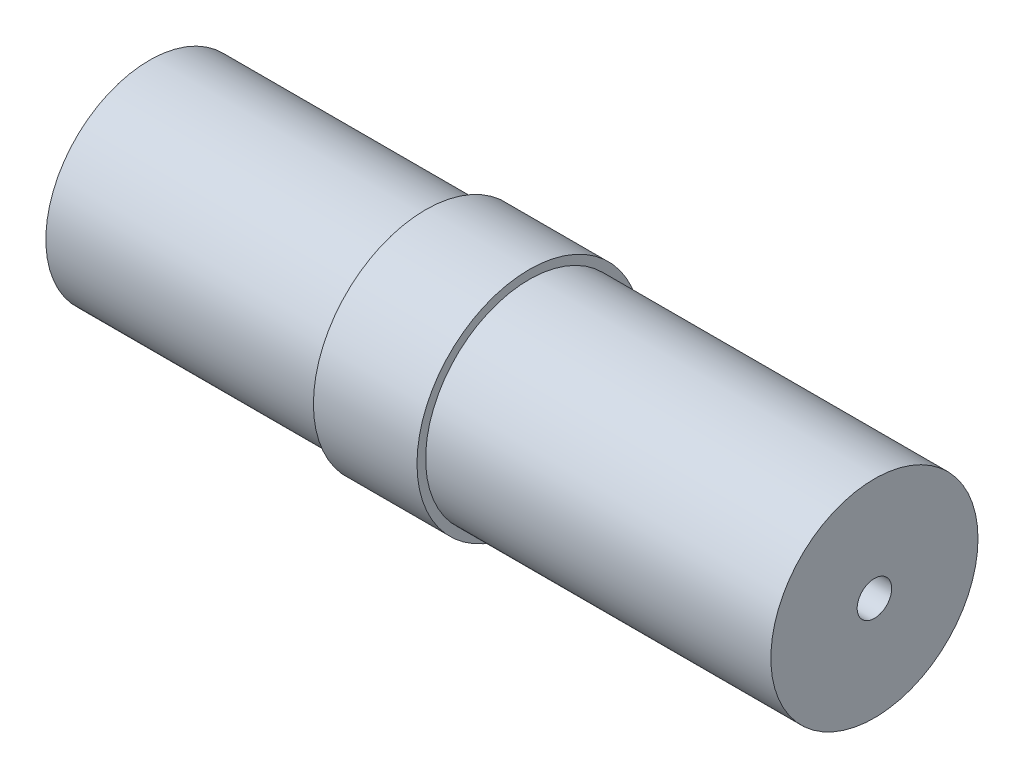
SolidWorks part; units mm, degrees
material "Tantalum"
ref_plane "Front Plane" through (0, 0, 0) normal (0, 0, 1) x (1, 0, 0)
ref_plane "Top Plane" through (0, 0, 0) normal (0, 1, 0) x (1, 0, 0)
ref_plane "Right Plane" through (0, 0, 0) normal (1, 0, 0) x (0, 0, -1)
sketch "Sketch1" plane through (0, 0, 0) normal (0, 0, 1) x (1, 0, 0)
  line L2 (11, 3.25) -> (-10, 3.25) construction
  line L3 (10, 0.5) -> (11, 0.5)
  line L4 (10, 0.5) -> (10, 2.25)
  line L5 (10, 2.25) -> (-10, 2.25)
  line L9 (-10, 2.25) -> (-10, 3.25) construction
  line L18 (1, 3.25) -> (1, 3)
  line L19 (1, 3) -> (11, 3)
  line L20 (11, 3) -> (11, 0.5)
  line L21 (1, 3) -> (-10, 3) construction
  line L22 (-2, 3.25) -> (-2, 3)
  line L23 (-10, 3) -> (-10, 2.25)
  line L24 (1, 3.25) -> (-2, 3.25)
  line L25 (-2, 3) -> (-10, 3)
  dimension "D1" = 3.25
  dimension "D2" = 2.75
  dimension "D3" = 1
  dimension "D4" = 1
  dimension "D5" = 0.25
  dimension "D6" = 10
  dimension "D7" = 8
  dimension "D8" = 3
  dimension "D9" = 20
ref_axis "Axis1" through (13.5, 0, 0) along (-1, 0, 0)
revolve "Revolve1" add sketch "Sketch1" angle 360 about axis through (13.5, 0, 0) along (-1, 0, 0)
other "#12-28 Machine Threads Stud1" [suppressed] parameters "D1"=5.4864, "D2"=10, "D3"=8, "D4"=6
sketch "Sketch15" plane through (-42.5, 0, 0) normal (0, 1, 0) x (0, 0, -1)
  line L5 (0, -14.3089) -> (0, 0) construction
  line L6 (2.2022, 0) -> (2.7432, -0.541)
  line L9 (2.7432, -0.541) -> (2.7432, -8)
  line L10 (2.2022, 0) -> (3, 0)
  line L11 (3, 0) -> (3, -8)
  line L12 (2.7432, -8) -> (3, -8)
  dimension "Minor Diameter" = 4.4044
  dimension "Major Diameter" = 5.4864
  dimension "Thread Length" = 8
  dimension "Cylinder Diameter" = 6
  dimension "Chamfer Angle" = 45
cosmetic thread "Stud Thread1" [suppressed] parameters "D1"=8, "D2"=4.4044
thread "Thread5" [suppressed] pitch 0.8 start angle 0, offset 0, length 8, pitch 0.8, diameter 5.4864
ref_plane "Plane6" through (-41.959, 0, -2.7432) normal (0, -1, 0) x (0, 0, -1)
sketch "Thread Profile6" plane through (-41.959, 0, -2.7432) normal (0, -1, 0) x (0, 0, -1)
  line L0 (0, 0) -> (0, 0.8) construction
  line L1 (0, 0) -> (0.433, 0.25)
  line L2 (0.433, 0.25) -> (0.433, 0.35)
  line L3 (0.433, 0.35) -> (0, 0.6)
  line L4 (0.433, 0.3) -> (0, 0.3) construction
  line L11 (0, 0) -> (0, 0.6)
  point P2 (0, 0)
  dimension "Pitch" = 0.8
  dimension "Profile_Angle" = 60
  dimension "Profile_Land" = 0.1
  dimension "Profile_Height" = 0.433
